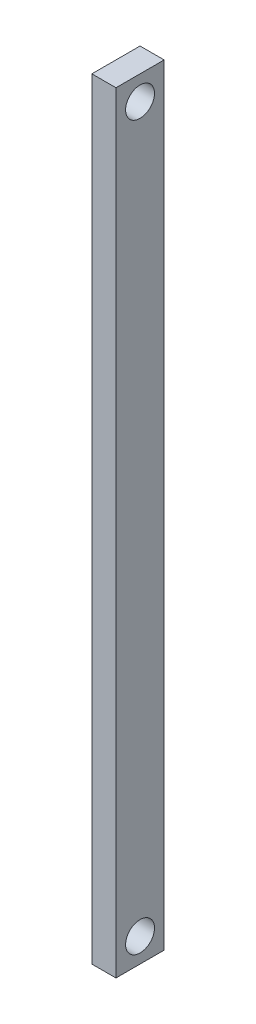
SolidWorks part; units mm, degrees
ref_plane "Front Plane" through (0, 0, 0) normal (0, 0, 1) x (1, 0, 0)
ref_plane "Top Plane" through (0, 0, 0) normal (0, 1, 0) x (1, 0, 0)
ref_plane "Right Plane" through (0, 0, 0) normal (1, 0, 0) x (0, 0, -1)
sketch "Sketch1" plane through (0, 0, 0) normal (1, 0, 0) x (0, 0, -1)
  line L1 (-5, -80) -> (5, -80)
  line L2 (-5, -80) -> (-5, 80)
  line L3 (-5, 80) -> (5, 80)
  line L4 (5, -80) -> (5, 80)
  line L5 (-5, -80) -> (5, 80) construction
  line L6 (-5, 80) -> (5, -80) construction
  point P0 (0, 0)
  dimension "D1" = 10
  dimension "D2" = 160
extrude "Boss-Extrude1" add sketch "Sketch1" along normal blind 5
sketch "Sketch3" plane through (5, 0, 0) normal (1, 0, 0) x (0, 0, -1)
  circle A0 centre (0, 75) radius 3
  circle A1 centre (0, -75) radius 3
  dimension "D1" = 75
  dimension "D2" = 2
extrude "Cut-Extrude2" cut sketch "Sketch3" against normal up to surface (5 mm away) up to face at (0, 0, 0)
